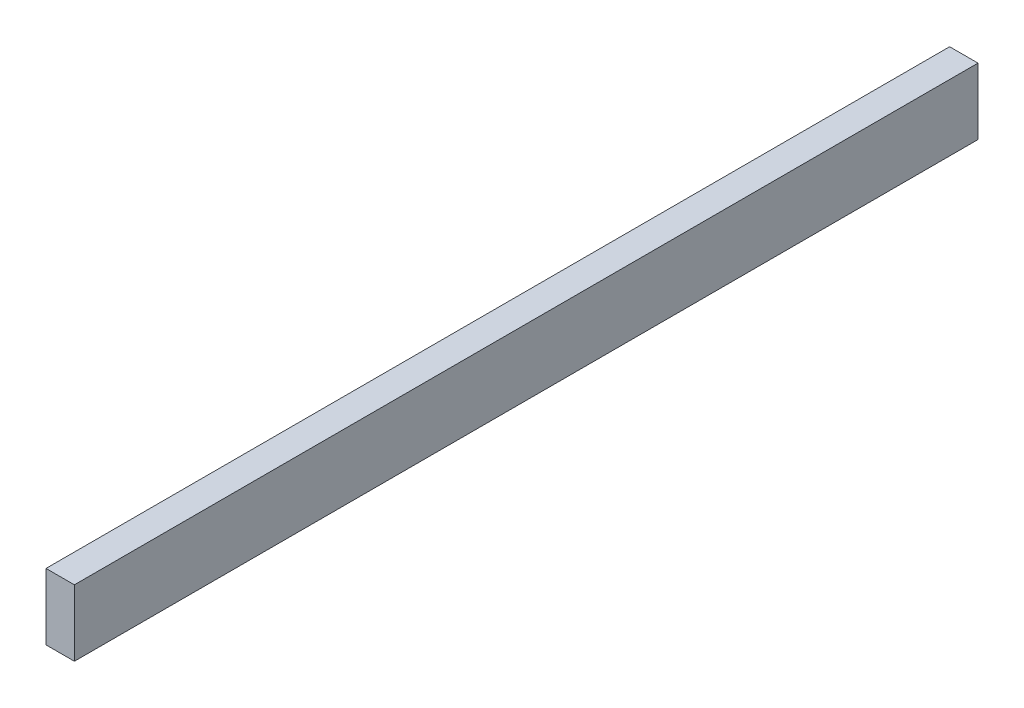
SolidWorks part; units mm, degrees
material "Pine"
ref_plane "Front Plane" through (0, 0, 0) normal (0, 0, 1) x (1, 0, 0)
ref_plane "Top Plane" through (0, 0, 0) normal (0, 1, 0) x (1, 0, 0)
ref_plane "Right Plane" through (0, 0, 0) normal (1, 0, 0) x (0, 0, -1)
sketch "Sketch1" plane through (0, 0, 0) normal (0, 0, 1) x (1, 0, 0)
  line L1 (-16.9556, 37.5347) -> (21.1444, 37.5347)
  line L2 (-16.9556, 37.5347) -> (-16.9556, -51.3653)
  line L3 (-16.9556, -51.3653) -> (21.1444, -51.3653)
  line L4 (21.1444, 37.5347) -> (21.1444, -51.3653)
  dimension "D1" = 38.1
  dimension "D2" = 88.9
extrude "Boss-Extrude1" add sketch "Sketch1" along normal blind 1212.85
